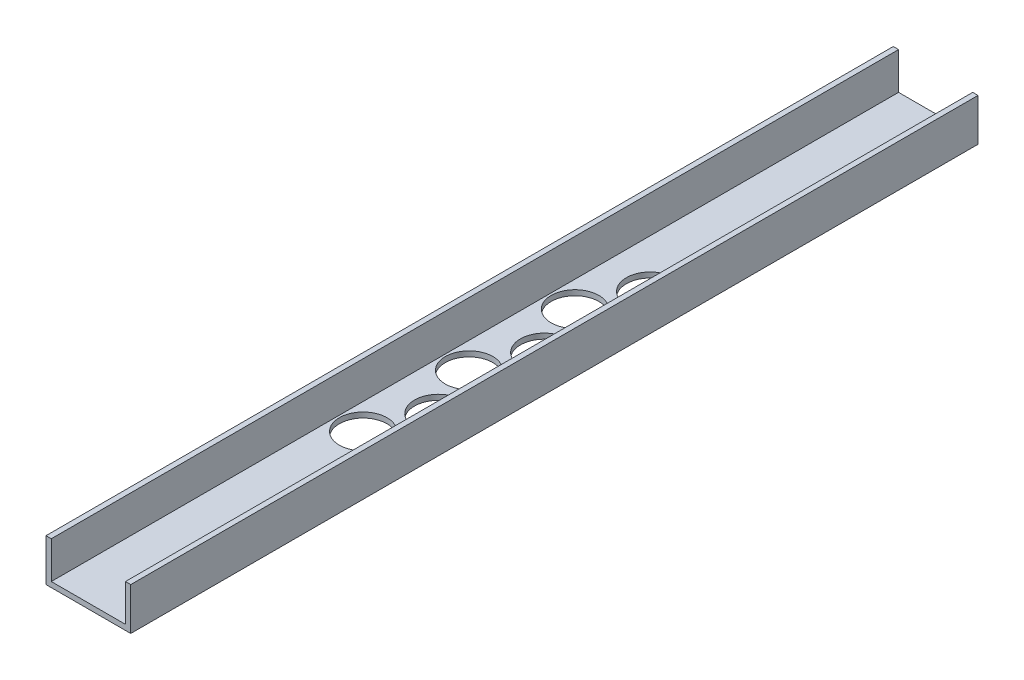
SolidWorks part; units mm, degrees
material "6063-T6"
ref_plane "Front" through (0, 0, 0) normal (0, 0, 1) x (1, 0, 0)
ref_plane "Top" through (0, 0, 0) normal (0, 1, 0) x (1, 0, 0)
ref_plane "Right" through (0, 0, 0) normal (1, 0, 0) x (0, 0, -1)
sketch "Sketch1" plane through (0, 0, 0) normal (0, 0, 1) x (1, 0, 0)
  line L0 (47.625, 3.175) -> (47.625, 25.4)
  line L1 (0, 0) -> (50.8, 0)
  line L2 (0, 0) -> (0, 25.4)
  line L4 (50.8, 0) -> (50.8, 25.4)
  line L5 (3.175, 3.175) -> (47.625, 3.175)
  line L6 (3.175, 3.175) -> (3.175, 25.4)
  line L7 (50.8, 25.4) -> (47.625, 25.4)
  line L8 (0, 25.4) -> (3.175, 25.4)
  dimension "D1" = 25.4
  dimension "D2" = 50.8
  dimension "D3" = 3.175
extrude "Boss-Extrude1" add sketch "Sketch1" along normal blind 508
sketch "Sketch2" plane through (0, 3.175, 0) normal (0, 1, 0) x (1, 0, 0)
  line L0 (4.445, -336.55) -> (3.175, -336.55) construction
  line L1 (3.175, -508) -> (3.175, 0) construction
  line L2 (46.355, -304.8) -> (47.625, -304.8) construction
  line L3 (47.625, -508) -> (47.625, 0) construction
  line L4 (47.625, -508) -> (3.175, -508) construction
  circle A0 centre (18.7325, -336.55) radius 14.2875
  circle A1 centre (32.0675, -304.8) radius 14.2875
  circle A2 centre (18.7325, -273.05) radius 14.2875
  circle A3 centre (32.0675, -241.3) radius 14.2875
  circle A4 centre (18.7325, -209.55) radius 14.2875
  circle A5 centre (32.0675, -177.8) radius 14.2875
  dimension "D1" = 28.575
  dimension "D3" = 28.575
  dimension "D2" = 1.27
  dimension "D4" = 31.75
  dimension "D5" = 171.45
  dimension "D6" = 3
extrude "Cut-Extrude1" cut sketch "Sketch2" against normal up to next
